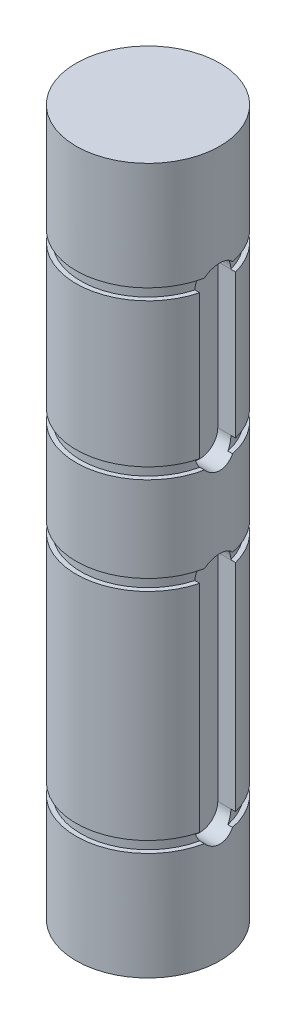
SolidWorks part; units mm, degrees
material "AISI 1020"
ref_plane "Front Plane" through (0, 0, 0) normal (0, 0, 1) x (1, 0, 0)
ref_plane "Top Plane" through (0, 0, 0) normal (0, 1, 0) x (1, 0, 0)
ref_plane "Right Plane" through (0, 0, 0) normal (1, 0, 0) x (0, 0, -1)
sketch "Sketch1" plane through (0, 0, 0) normal (0, 1, 0) x (1, 0, 0)
  circle A0 centre (0, 0) radius 6.35
extrude "Boss-Extrude1" add sketch "Sketch1" along normal blind 62.3062 contours A0
sketch "Sketch2" plane through (0, 0, 0) normal (1, 0, 0) x (0, 0, -1)
  line L0 (6.35, 62.3062) -> (-6.35, 62.3062) construction
  line L1 (-30.9495, 52.7812) -> (-5.9436, 52.7812)
  line L2 (-30.9495, 52.7812) -> (-30.9495, 51.7906)
  line L3 (-30.9495, 51.7906) -> (-5.9436, 51.7906)
  line L4 (-5.9436, 52.7812) -> (-5.9436, 51.7906)
  line L5 (-6.35, 62.3062) -> (-6.35, 0) construction
  line L6 (0, 57.348) -> (0, 46.5856) construction
  dimension "D1" = 9.525
  dimension "D2" = 0.9906
  dimension "D3" = 0.4064
revolve "Cut-Revolve1" cut sketch "Sketch2" angle 360 about L6
sketch "Sketch3" plane through (0, 0, 0) normal (1, 0, 0) x (0, 0, -1)
  line L0 (6.35, 51.7906) -> (-6.35, 51.7906) construction
  line L1 (-29.4898, 39.0906) -> (-5.9436, 39.0906)
  line L2 (-29.4898, 39.0906) -> (-29.4898, 38.1)
  line L3 (-29.4898, 38.1) -> (-5.9436, 38.1)
  line L4 (-5.9436, 39.0906) -> (-5.9436, 38.1)
  line L5 (-6.35, 51.7906) -> (-6.35, 0) construction
  line L6 (0, 44.893) -> (0, 33.6519) construction
  dimension "D1" = 12.7
  dimension "D2" = 0.9906
  dimension "D3" = 0.4064
revolve "Cut-Revolve2" cut sketch "Sketch3" angle 360 about L6
sketch "Sketch4" plane through (0, 0, 0) normal (1, 0, 0) x (0, 0, -1)
  line L0 (6.35, 38.1) -> (-6.35, 38.1) construction
  line L1 (-24.602, 30.5562) -> (-5.9436, 30.5562)
  line L2 (-24.602, 30.5562) -> (-24.602, 29.5656)
  line L3 (-24.602, 29.5656) -> (-5.9436, 29.5656)
  line L4 (-5.9436, 30.5562) -> (-5.9436, 29.5656)
  line L5 (-6.35, 38.1) -> (-6.35, 0) construction
  line L6 (0, 32.8864) -> (0, 25.8354) construction
  dimension "D1" = 7.5438
  dimension "D2" = 0.9906
  dimension "D3" = 0.4064
revolve "Cut-Revolve3" cut sketch "Sketch4" angle 360 about L6
sketch "Sketch5" plane through (0, 0, 0) normal (1, 0, 0) x (0, 0, -1)
  line L0 (6.35, 29.5656) -> (-6.35, 29.5656) construction
  line L1 (-27.8341, 10.5156) -> (-5.9436, 10.5156)
  line L2 (-27.8341, 10.5156) -> (-27.8341, 9.525)
  line L3 (-27.8341, 9.525) -> (-5.9436, 9.525)
  line L4 (-5.9436, 10.5156) -> (-5.9436, 9.525)
  line L5 (-6.35, 29.5656) -> (-6.35, 0) construction
  line L6 (0, 12.8889) -> (0, 4.9455) construction
  dimension "D1" = 21.8905
  dimension "D2" = 19.05
  dimension "D3" = 0.9906
  dimension "D4" = 0.4064
revolve "Cut-Revolve4" cut sketch "Sketch5" angle 360 about L6
ref_plane "Plane1" through (6.35, 0, 0) normal (1, 0, 0) x (0, 0, -1)
sketch "Sketch6" plane through (6.35, 0, 0) normal (1, 0, 0) x (0, 0, -1)
  line L0 (0, 51.7906) -> (0, 39.0906) construction
  line L1 (6.35, 51.7906) -> (-6.35, 51.7906) construction
  line L2 (-5.9436, 39.0906) -> (5.9436, 39.0906) construction
  line L3 (1.5875, 51.7906) -> (1.5875, 39.0906)
  line L4 (-1.5875, 51.7906) -> (-1.5875, 39.0906)
  arc A0 (1.5875, 51.7906) -> (-1.5875, 51.7906) centre (0, 51.7906) ccw
  arc A1 (-1.5875, 39.0906) -> (1.5875, 39.0906) centre (0, 39.0906) ccw
  point P6 (0, 45.4406)
  dimension "D1" = 3.175
extrude "Cut-Extrude1" cut sketch "Sketch6" against normal blind 1.778
sketch "Sketch7" plane through (6.35, 0, 0) normal (1, 0, 0) x (0, 0, -1)
  line L0 (0, 29.5656) -> (0, 10.5156) construction
  line L1 (6.35, 29.5656) -> (-6.35, 29.5656) construction
  line L2 (-5.9436, 10.5156) -> (5.9436, 10.5156) construction
  line L3 (1.5875, 29.5656) -> (1.5875, 10.5156)
  line L4 (-1.5875, 29.5656) -> (-1.5875, 10.5156)
  arc A0 (1.5875, 29.5656) -> (-1.5875, 29.5656) centre (0, 29.5656) ccw
  arc A1 (-1.5875, 10.5156) -> (1.5875, 10.5156) centre (0, 10.5156) ccw
  point P6 (0, 20.0406)
  dimension "D1" = 3.175
extrude "Cut-Extrude2" cut sketch "Sketch7" against normal blind 1.778
